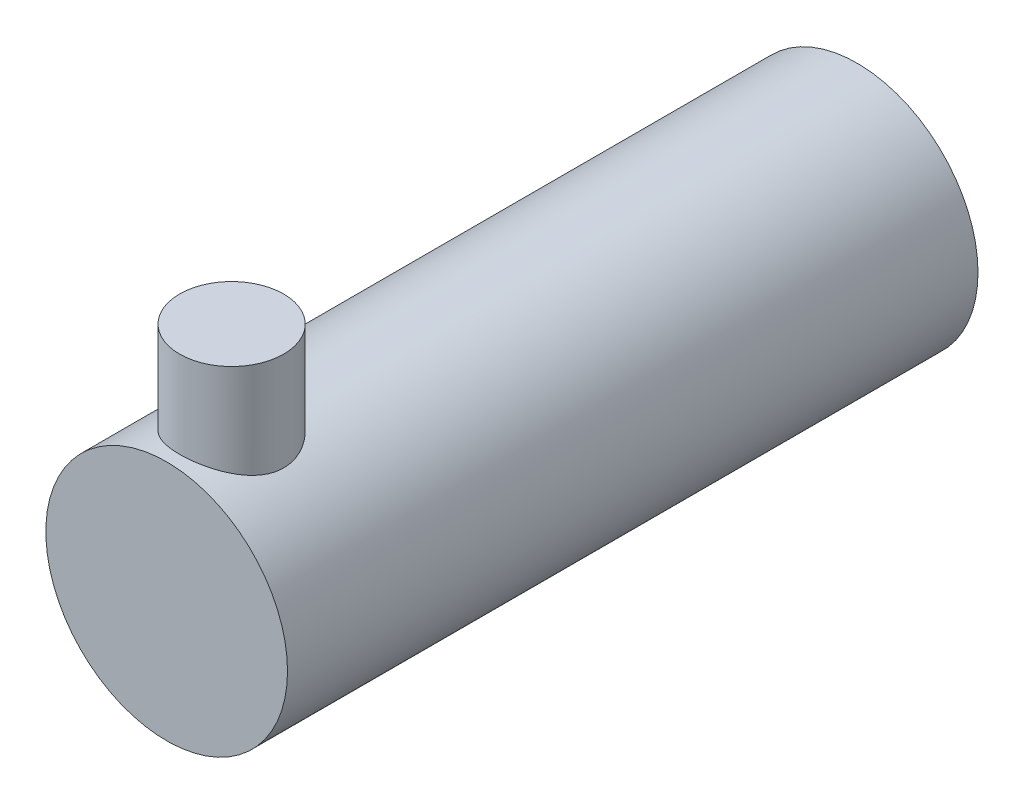
SolidWorks part; units mm, degrees
ref_plane "Ön Düzlem" through (0, 0, 0) normal (0, 0, 1) x (1, 0, 0)
ref_plane "Üst Düzlem" through (0, 0, 0) normal (0, 1, 0) x (1, 0, 0)
ref_plane "Sağ Düzlem" through (0, 0, 0) normal (1, 0, 0) x (0, 0, -1)
sketch "Sketch1" plane through (0, 0, 0) normal (0, 0, 1) x (1, 0, 0)
  circle A0 centre (0, 0) radius 14
  dimension "D1" = 28
extrude "Boss-Extrude1" add sketch "Sketch1" along normal blind 80
ref_plane "Plane1" through (0, 11.0594, 0) normal (0, 1, 0) x (1, 0, 0)
sketch "Sketch2" plane through (0, 11.0594, 0) normal (0, 1, 0) x (1, 0, 0)
  circle A0 centre (0, -72.4737) radius 6.032
extrude "Boss-Extrude2" add sketch "Sketch2" along normal blind 13 contours A0
